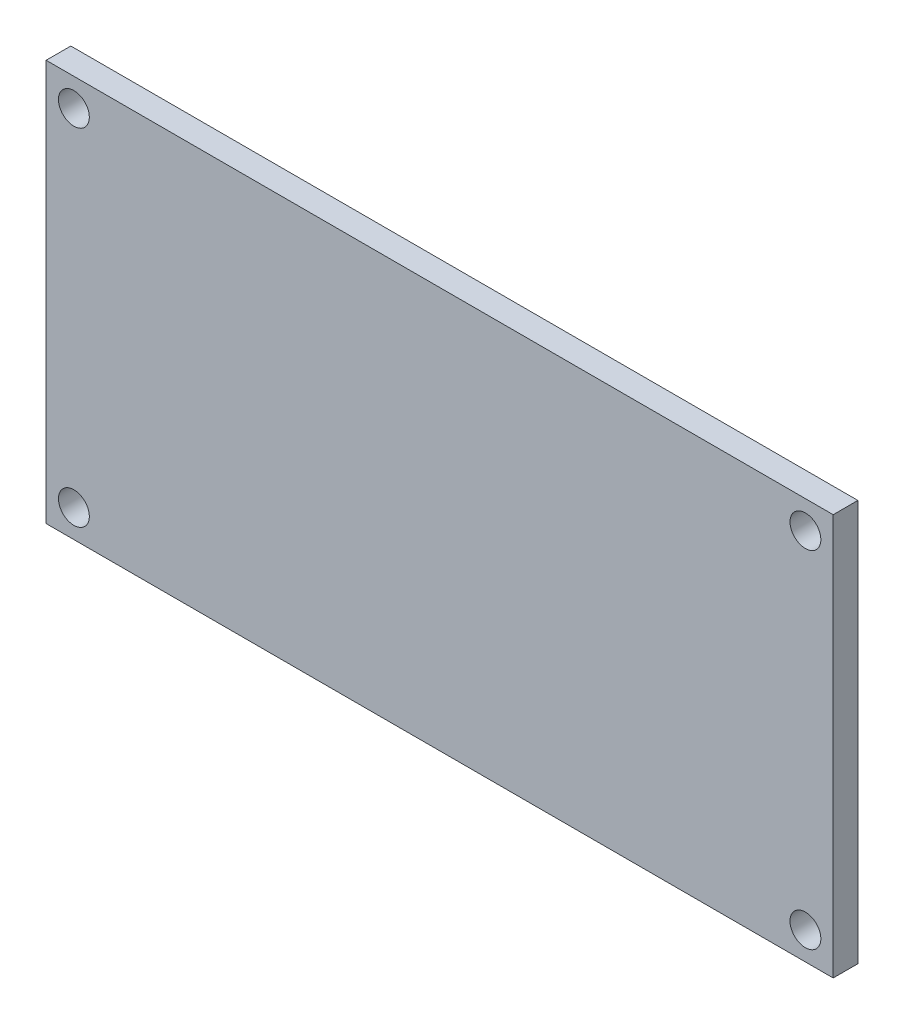
SolidWorks part; units mm, degrees
ref_plane "Front Plane" through (0, 0, 0) normal (0, 0, 1) x (1, 0, 0)
ref_plane "Top Plane" through (0, 0, 0) normal (0, 1, 0) x (1, 0, 0)
ref_plane "Right Plane" through (0, 0, 0) normal (1, 0, 0) x (0, 0, -1)
sketch "Sketch1" plane through (0, 0, 0) normal (0, 0, 1) x (1, 0, 0)
  line L0 (0, 13) -> (0, -13) construction
  line L1 (-25.5, -13) -> (25.5, -13)
  line L2 (-25.5, -13) -> (-25.5, 13)
  line L3 (-25.5, 13) -> (25.5, 13)
  line L4 (25.5, -13) -> (25.5, 13)
  line L5 (-25.5, -13) -> (25.5, 13) construction
  line L6 (-25.5, 13) -> (25.5, -13) construction
  line L7 (-25.5, 0) -> (25.5, 0) construction
  circle A0 centre (-23.7, 11.2) radius 1
  circle A1 centre (-23.7, -11.2) radius 1
  circle A2 centre (23.7, -11.2) radius 1
  circle A3 centre (23.7, 11.2) radius 1
  point P0 (0, 0)
  dimension "D3" = 2
  dimension "D1" = 26
  dimension "D2" = 51
  dimension "D4" = 1.8
  dimension "D5" = 1.8
extrude "Boss-Extrude1" add sketch "Sketch1" along normal blind 1.6
